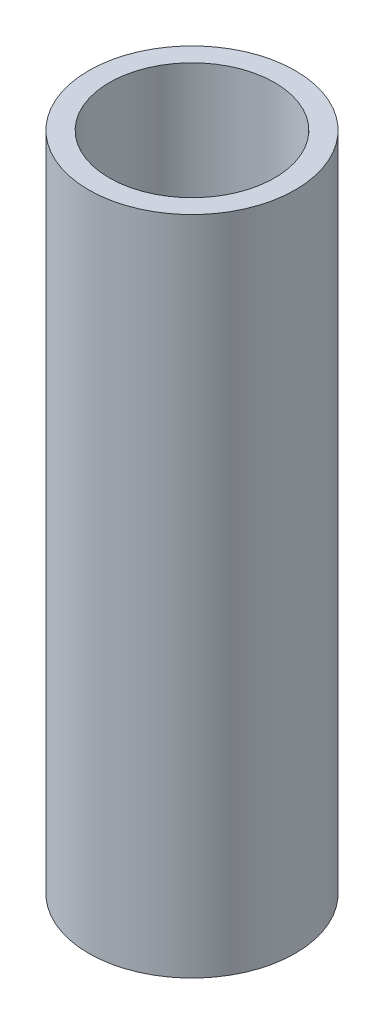
SolidWorks part; units mm, degrees
ref_plane "Front Plane" through (0, 0, 0) normal (0, 0, 1) x (1, 0, 0)
ref_plane "Top Plane" through (0, 0, 0) normal (0, 1, 0) x (1, 0, 0)
ref_plane "Right Plane" through (0, 0, 0) normal (1, 0, 0) x (0, 0, -1)
sketch "Sketch1" plane through (0, 0, 0) normal (0, 1, 0) x (1, 0, 0)
  circle A0 centre (0, 0) radius 2.5
  circle A1 centre (0, 0) radius 2
extrude "Boss-Extrude1" add sketch "Sketch1" along normal blind 16
